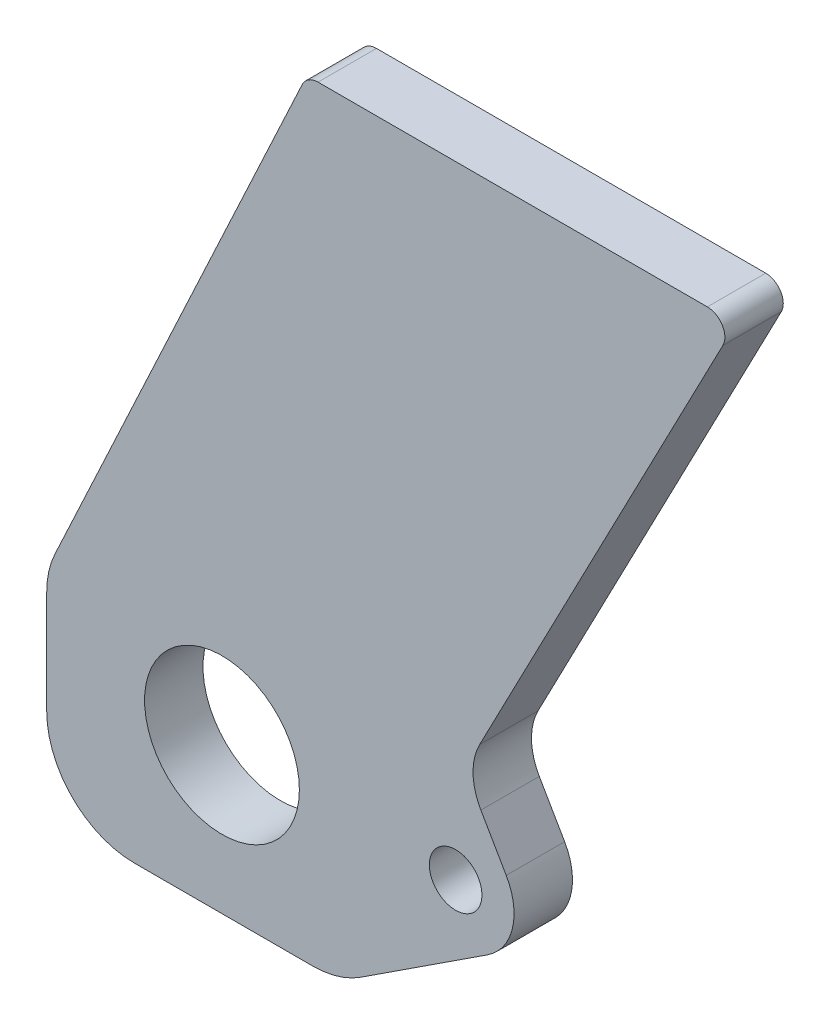
SolidWorks part; units mm, degrees
ref_plane "Plane1" through (0, 0, 0) normal (0, 0, 1) x (1, 0, 0)
ref_plane "Plane2" through (0, 0, 0) normal (0, 1, 0) x (1, 0, 0)
ref_plane "Plane3" through (0, 0, 0) normal (1, 0, 0) x (0, 0, -1)
sketch "Sketch1" plane through (0, 0, 0) normal (0, 0, 1) x (1, 0, 0)
  line L0 (44.5, 0) -> (-30, 0) construction
  line L1 (45.4668, -8.3734) -> (23.7371, -22.5601)
  line L2 (15.5369, -25) -> (-15, -25)
  line L3 (16.4436, 106.5) -> (83.0885, 106.5)
  line L4 (0, 0) -> (-65, 0) construction
  line L5 (48.6603, 5) -> (44.3224, 12.5133)
  line L6 (-30, 7.6746) -> (-30, -10)
  line L7 (-28.5946, 14.0139) -> (13.7247, 104.7679)
  line L9 (0, 0) -> (0, -19.4076) construction
  line L16 (44.1126, 22.1308) -> (85.7496, 102.1148)
  circle A0 centre (0, 0) radius 13.25
  arc A1 (48.6603, 5) -> (45.4668, -8.3734) centre (40, 0) cw
  arc A2 (-30, -10) -> (-15, -25) centre (-15, -10) ccw
  arc A3 (44.1126, 22.1308) -> (44.3224, 12.5133) centre (52.9827, 17.5133) ccw
  arc A4 (-28.5946, 14.0139) -> (-30, 7.6746) centre (-15, 7.6746) ccw
  arc A5 (83.0885, 106.5) -> (85.7496, 102.1148) centre (83.0885, 103.5) cw
  arc A6 (13.7247, 104.7679) -> (16.4436, 106.5) centre (16.4436, 103.5) cw
  circle A7 centre (40, 0) radius 4.5
  arc A8 (23.7371, -22.5601) -> (15.5369, -25) centre (15.5369, -10) cw
  point P19 (-30, 11)
  point P23 (88.0324, 106.5)
  point P27 (14.5324, 106.5)
  point P32 (20, -25)
  point P38 (-30, 11)
  dimension "D4" = 10
  dimension "D5" = 26.5
  dimension "D8" = 2.5
  dimension "D7" = 25
  dimension "D10" = 15
  dimension "D11" = 60
  dimension "D12" = 73.5
  dimension "D13" = 10
  dimension "D15" = 15
  dimension "D17" = 40
  dimension "D16" = 3
  dimension "D18" = 9
  dimension "D2" = 106.5
  dimension "D3" = 11
  dimension "D6" = 25
  dimension "D9" = 20
  dimension "D1" = 30
extrude "Base-Extrude" add sketch "Sketch1" along normal blind 10
hole_wizard "M10 gevindhul" [suppressed] positions "Sketch3" profile "Sketch2" legacy
sketch "Sketch3" plane through (0, 0, 0) normal (0, 0, -1) x (-1, 0, 0)
  line L0 (30, 7.6746) -> (30, -15) construction
  line L1 (15, -30) -> (-15, -30) construction
  line L2 (0, 0) -> (-12, 27.4955) construction
  point P0 (-12, 27.4955)
  dimension "D1" = 30
  dimension "D2" = 42
  dimension "D3" = 57.4955
  dimension "D4" = 23.578
sketch "Sketch2" plane through (12, 27.4955, 0) normal (1, 0, 0) x (0, 1, 0)
  line L0 (0, 0) -> (0, 10)
  line L1 (0, 10) -> (4.25, 10)
  line L2 (4.25, 10) -> (4.25, 0)
  line L3 (4.25, 0) -> (0, 0)
  line L4 (0, 110) -> (0, -10) construction
  dimension "Diameter" = 8.5
  dimension "Depth" = 10
cosmetic thread "Cosmetic Thread1" [suppressed] parameters "D1"=10, "D2"=10
